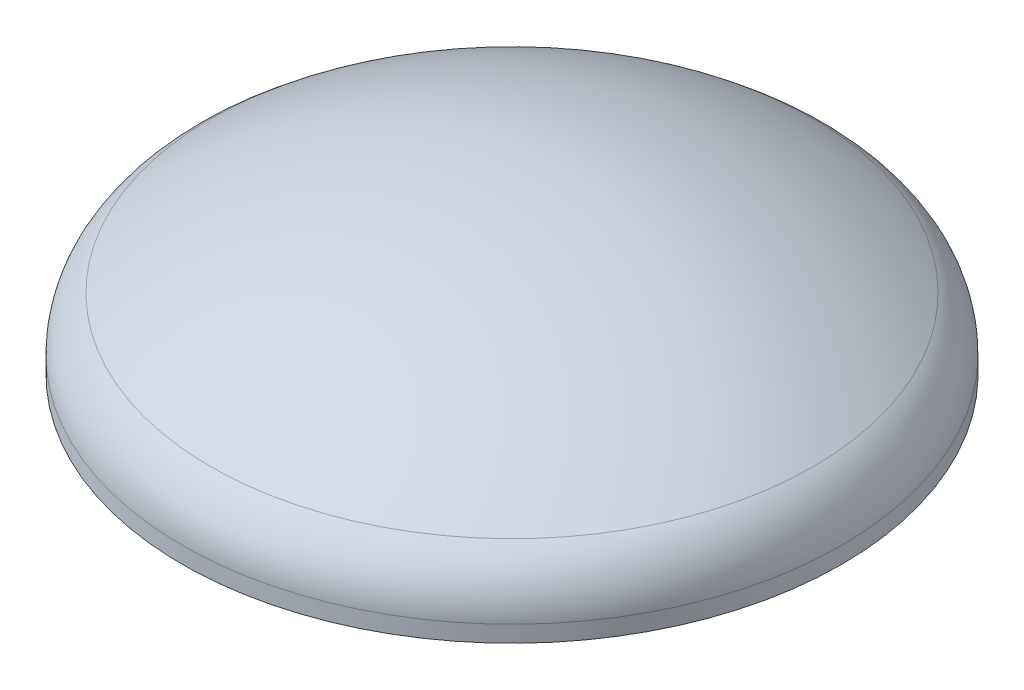
SolidWorks part; units mm, degrees
material "ASTM A36 Steel"
ref_plane "Front Plane" through (0, 0, 0) normal (0, 0, 1) x (1, 0, 0)
ref_plane "Top Plane" through (0, 0, 0) normal (0, 1, 0) x (1, 0, 0)
ref_plane "Right Plane" through (0, 0, 0) normal (1, 0, 0) x (0, 0, -1)
sketch "Sketch1" plane through (0, 0, 0) normal (0, 0, 1) x (1, 0, 0)
  line L0 (0, 254.5524) -> (-106.9532, 254.5524) construction
  line L1 (508, 25.4) -> (508, 0)
  line L2 (482.6, 25.4) -> (482.6, 0)
  line L3 (0, 254.5524) -> (0, 229.1524)
  line L4 (482.6, 0) -> (508, 0)
  arc A0 (0, 254.5524) -> (464.4571, 108.7782) centre (0, -558.2476) cw
  arc A1 (464.4571, 108.7782) -> (508, 25.4) centre (406.4, 25.4) cw
  arc A2 (0, 229.1524) -> (449.9429, 87.9337) centre (0, -558.2476) cw
  arc A3 (449.9429, 87.9337) -> (482.6, 25.4) centre (406.4, 25.4) cw
  dimension "D4" = 101.6
  dimension "D5" = 812.8
  dimension "D1" = 106.9532
  dimension "D2" = 508
  dimension "D3" = 25.4
  dimension "D6" = 25.4
revolve "Revolve1" add sketch "Sketch1" angle 360 about L3
sketch "Sketch3" plane through (0, 0, 0) normal (0, 1, 0) x (1, 0, 0)
  line L0 (0, 0) -> (0, 482.6)
  line L1 (0, 0) -> (482.6, 0)
  arc A1 (0, 482.6) -> (482.6, 0) centre (0, 0) cw
equation "\"D4@Sketch1\"=\"D2@Sketch1\"*2*0.1"
equation "\"D5@Sketch1\"=\"D2@Sketch1\"*2*0.8"
